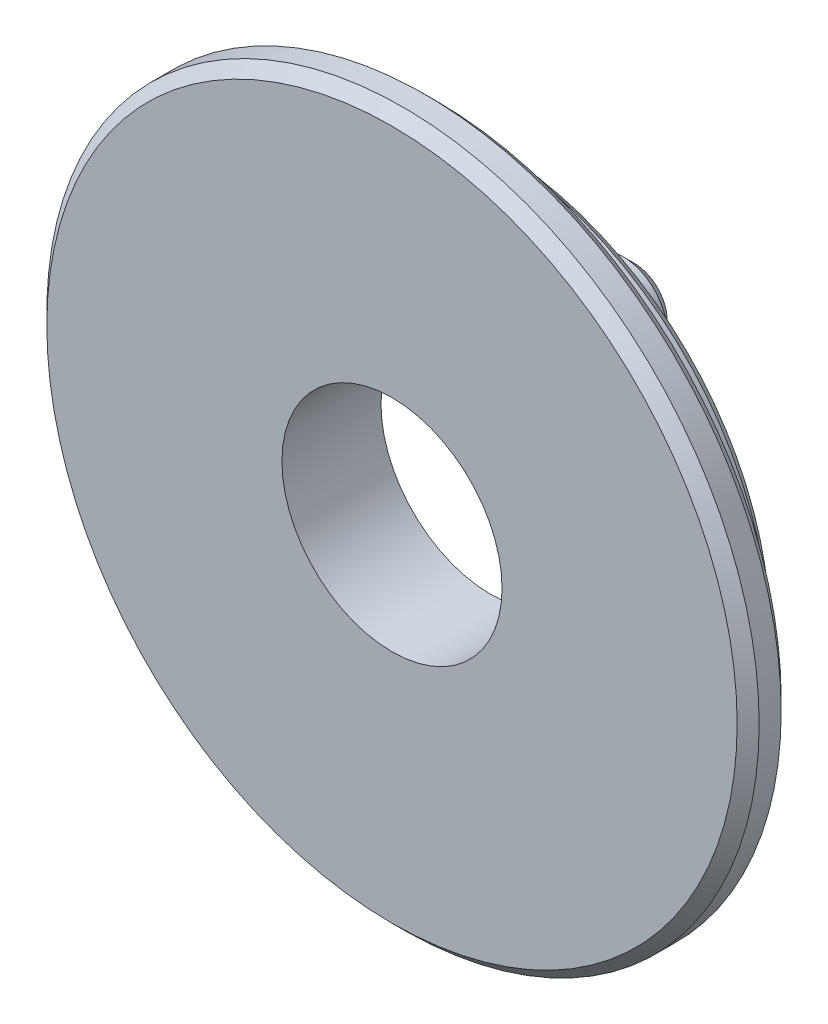
SolidWorks part; units mm, degrees
material "AISI 1020"
ref_plane "Front Plane" through (0, 0, 0) normal (0, 0, 1) x (1, 0, 0)
ref_plane "Top Plane" through (0, 0, 0) normal (0, 1, 0) x (1, 0, 0)
ref_plane "Right Plane" through (0, 0, 0) normal (1, 0, 0) x (0, 0, -1)
sketch "Sketch1" plane through (0, 0, 0) normal (0, 1, 0) x (1, 0, 0)
  line L0 (0, -17.8725) -> (0, 33.6003) construction
  line L1 (0, 0) -> (0, 2.25)
  line L2 (8.09, 0) -> (0, 0)
  line L3 (8.09, 0) -> (8.09, 1)
  line L4 (8.09, 1) -> (6.58, 1)
  line L8 (0, 2.25) -> (6.58, 2.25)
  line L9 (6.58, 1) -> (6.58, 2.25)
  dimension "D1" = 8.09
  dimension "D2" = 1
  dimension "D3" = 6.58
  dimension "D4" = 1.25
revolve "Revolve1" add sketch "Sketch1" angle 360 about L0
hole_wizard "M6x1.0 Tapped Hole1" positions "3DSketch1" profile "Sketch2" tap size "M6x1.0" standard "Ansi Metric"
sketch3d "3DSketch1"
  point P0 (0, 0, 0)
  point P4 (0, 0, 0)
sketch "Sketch2" plane through (0, 0, 0) normal (1, 0, 0) x (0, -1, 0)
  line L0 (0, 0) -> (0, 16.5022)
  line L1 (0, 16.5022) -> (2.5, 15)
  line L2 (2.5, 15) -> (2.5, 0)
  line L5 (2.5, 0) -> (0, 0)
  line L10 (0, 16.5022) -> (-2.5, 15) construction
  line L11 (0, -6.35) -> (0, 107.95) construction
  dimension "Tap Drill Dia." = 5
  dimension "Tap Drill Depth" = 15
  dimension "Drill Angle" = 118
cosmetic thread "Hole Thread1" parameters "D1"=2.25, "D2"=6
cosmetic thread "Hole Thread2" parameters "D1"=2.25, "D2"=6
sketch "Sketch3" plane through (0, 0, -2.25) normal (0, 0, -1) x (-1, 0, 0)
  line L0 (0, 0) -> (2.5745, 4.4592) construction
  line L1 (0, 0) -> (7.2375, 0) construction
  circle A0 centre (4.5, 0) radius 1
  circle A1 centre (-2.25, 3.8971) radius 1
  circle A2 centre (-2.25, -3.8971) radius 1
  dimension "D1" = 2
  dimension "D2" = 4.5
  dimension "D3" = 60
extrude "Extrude1" add sketch "Sketch3" along normal blind 1
chamfer "Chamfer1" distance 0.25 angle 45 6 edges at (-5.5, 0, -3.25) (1.25, -3.8971, -3.25) (3.25, 3.8971, -3.25) (8.09, 0, 0) (8.09, 0, -1) (6.58, 0, -2.25)
